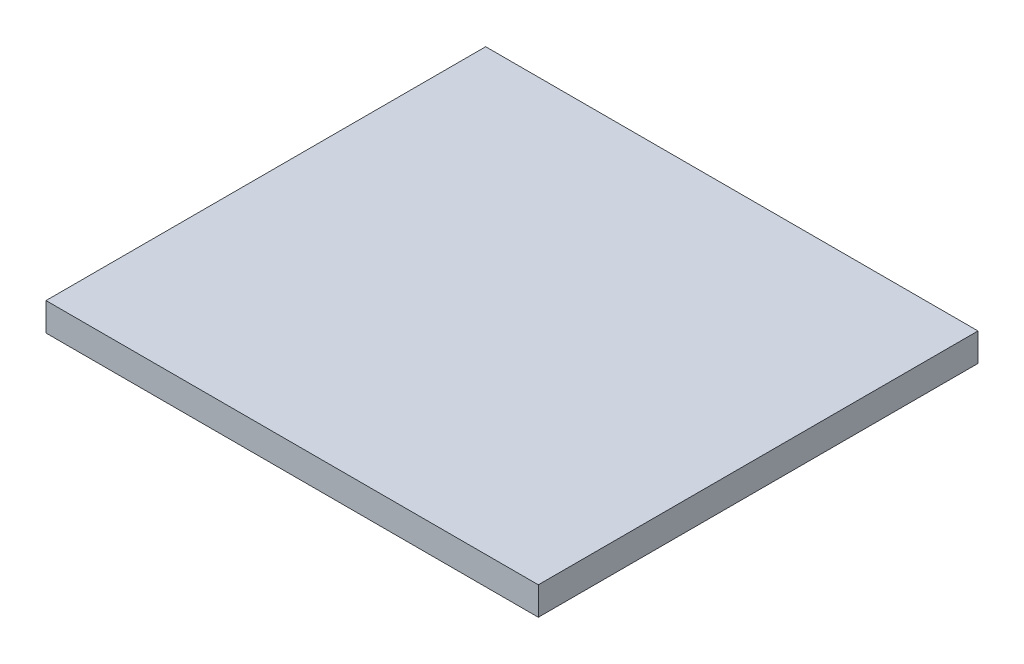
SolidWorks part; units mm, degrees
ref_plane "Front Plane" through (0, 0, 0) normal (0, 0, 1) x (1, 0, 0)
ref_plane "Top Plane" through (0, 0, 0) normal (0, 1, 0) x (1, 0, 0)
ref_plane "Right Plane" through (0, 0, 0) normal (1, 0, 0) x (0, 0, -1)
sketch "Sketch1" plane through (0, 0, 0) normal (0, 1, 0) x (1, 0, 0)
  line L1 (-333.1, 297.485) -> (333.1, 297.485)
  line L2 (-333.1, 297.485) -> (-333.1, -297.485)
  line L3 (-333.1, -297.485) -> (333.1, -297.485)
  line L4 (333.1, 297.485) -> (333.1, -297.485)
  line L5 (-333.1, 297.485) -> (333.1, -297.485) construction
  line L6 (-333.1, -297.485) -> (333.1, 297.485) construction
  point P0 (0, 0)
  dimension "D1" = 666.2
  dimension "D2" = 594.97
extrude "Boss-Extrude1" add sketch "Sketch1" along normal blind 38.1
